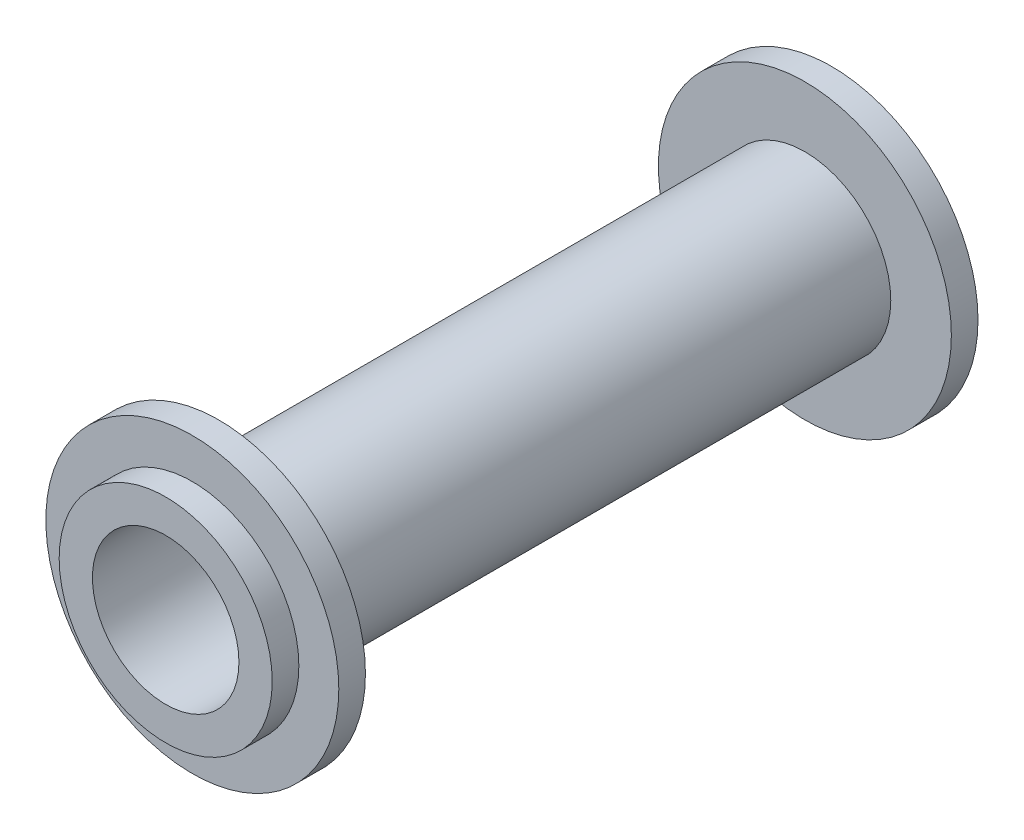
SolidWorks part; units mm, degrees
ref_plane "Front Plane" through (0, 0, 0) normal (0, 0, 1) x (1, 0, 0)
ref_plane "Top Plane" through (0, 0, 0) normal (0, 1, 0) x (1, 0, 0)
ref_plane "Right Plane" through (0, 0, 0) normal (1, 0, 0) x (0, 0, -1)
sketch "Sketch1" plane through (0, 0, 0) normal (1, 0, 0) x (0, 0, -1)
  line L0 (0, 5.5) -> (52, 5.5)
  line L1 (52, 5.5) -> (52, 8)
  line L2 (52, 8) -> (50, 8)
  line L3 (50, 8) -> (50, 11)
  line L4 (50, 11) -> (48, 11)
  line L5 (48, 11) -> (48, 6.45)
  line L6 (48, 6.45) -> (4, 6.45)
  line L7 (4, 6.45) -> (4, 11)
  line L8 (4, 11) -> (2, 11)
  line L9 (2, 11) -> (2, 8)
  line L10 (2, 8) -> (0, 8)
  line L11 (0, 8) -> (0, 5.5)
  line L12 (0, 0) -> (76.7895, 0) construction
  dimension "D1" = 5.5
  dimension "D2" = 6.45
  dimension "D3" = 8
  dimension "D4" = 11
  dimension "D5" = 2
  dimension "D6" = 2
  dimension "D7" = 44
revolve "Revolve1" add sketch "Sketch1" angle 360 about L12
